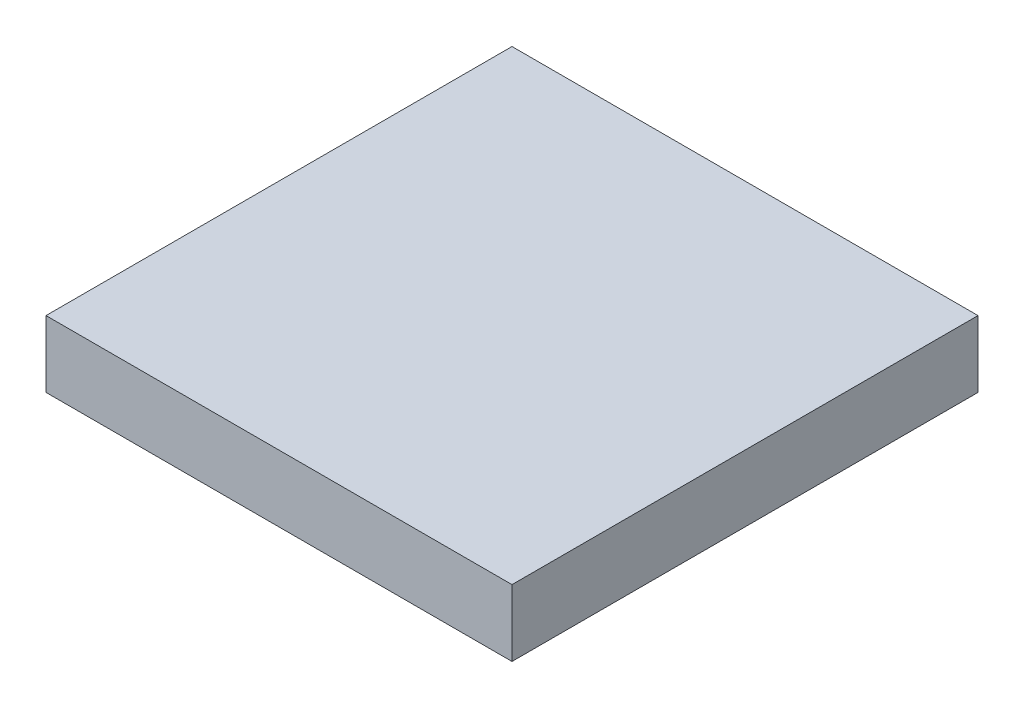
SolidWorks part; units mm, degrees
ref_plane "Front Plane" through (0, 0, 0) normal (0, 0, 1) x (1, 0, 0)
ref_plane "Top Plane" through (0, 0, 0) normal (0, 1, 0) x (1, 0, 0)
ref_plane "Right Plane" through (0, 0, 0) normal (1, 0, 0) x (0, 0, -1)
sketch "Sketch1" plane through (0, 0, 0) normal (0, 1, 0) x (1, 0, 0)
  line L0 (-35, 35) -> (35, -35) construction
  line L1 (-35, 35) -> (35, 35)
  line L2 (-35, 35) -> (-35, -35)
  line L3 (-35, -35) -> (35, -35)
  line L4 (35, 35) -> (35, -35)
  dimension "D1" = 70
  dimension "D2" = 70
extrude "Boss-Extrude1" add sketch "Sketch1" along normal blind 10
